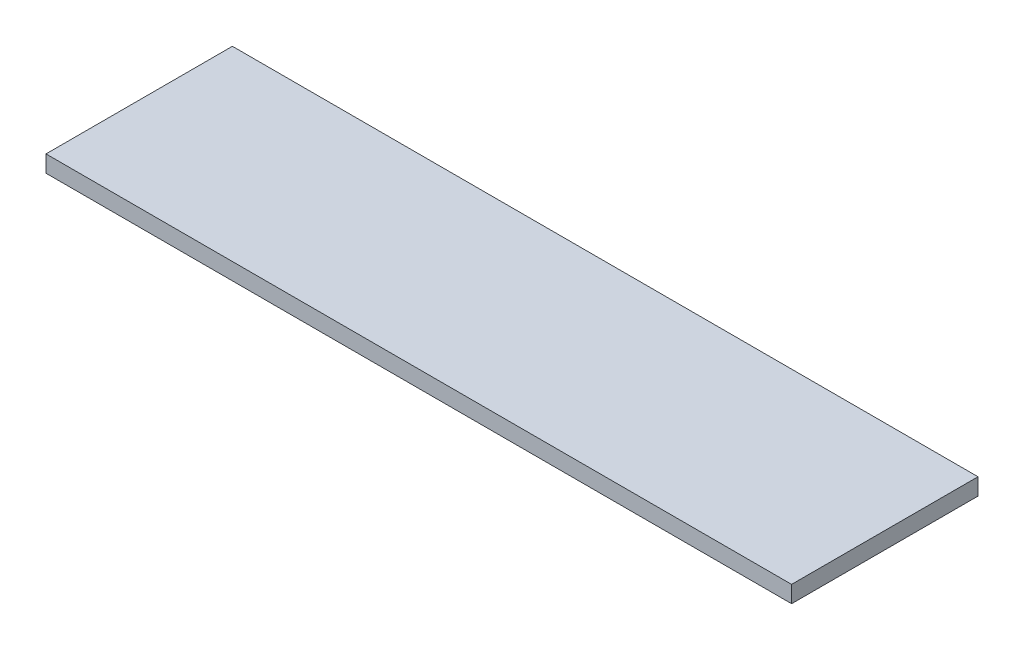
SolidWorks part; units mm, degrees
ref_plane "前视基准面" through (0, 0, 0) normal (0, 0, 1) x (1, 0, 0)
ref_plane "上视基准面" through (0, 0, 0) normal (0, 1, 0) x (1, 0, 0)
ref_plane "右视基准面" through (0, 0, 0) normal (1, 0, 0) x (0, 0, -1)
sketch "草图1" plane through (0, 0, 0) normal (0, 1, 0) x (1, 0, 0)
  line L1 (0, 0) -> (80, 0)
  line L2 (0, 0) -> (0, 20)
  line L3 (0, 20) -> (80, 20)
  line L4 (80, 0) -> (80, 20)
  dimension "D1" = 80
  dimension "D2" = 20
extrude "凸台-拉伸1" add sketch "草图1" along normal blind 1.8
